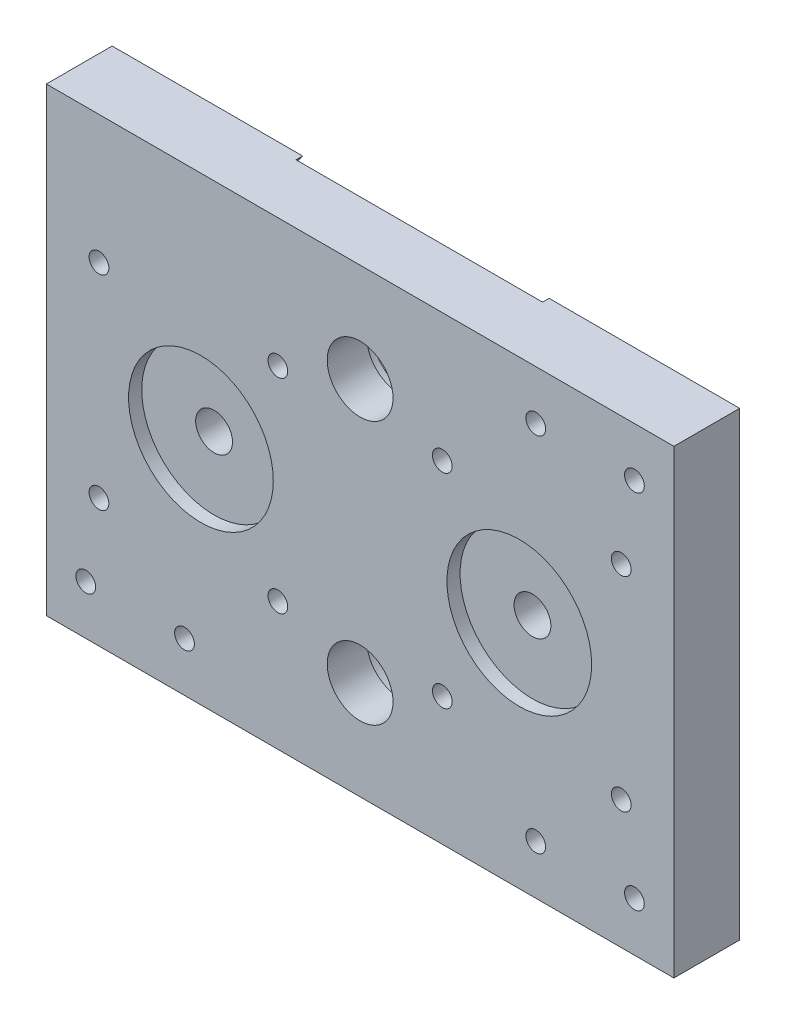
SolidWorks part; units mm, degrees
ref_plane "Front Plane" through (0, 0, 0) normal (0, 0, 1) x (1, 0, 0)
ref_plane "Top Plane" through (0, 0, 0) normal (0, 1, 0) x (1, 0, 0)
ref_plane "Right Plane" through (0, 0, 0) normal (1, 0, 0) x (0, 0, -1)
sketch "Sketch1" plane through (0, 0, 0) normal (0, 0, 1) x (1, 0, 0)
  line L0 (0, 0) -> (0, 40) construction
  line L2 (12.5, -15) -> (-12.5, -15)
  line L3 (12.5, -15) -> (12.5, 55)
  line L4 (12.5, 55) -> (-12.5, 55)
  line L5 (-12.5, -15) -> (-12.5, 55)
  line L6 (12.5, -15) -> (-12.5, 55) construction
  line L7 (12.5, 55) -> (-12.5, -15) construction
  circle A0 centre (0, 40) radius 7.9375
  circle A1 centre (0, 0) radius 7.9375
  point P5 (0, 20)
  dimension "D2" = 15.875
  dimension "D1" = 40
  dimension "D3" = 70
  dimension "D4" = 25
extrude "Boss-Extrude1" add sketch "Sketch1" along normal blind 10
sketch "Sketch2" plane through (0, 0, 10) normal (0, 0, 1) x (1, 0, 0)
  line L0 (12.5, 55) -> (-12.5, 55) construction
  line L1 (-47.7, 55) -> (-8.2, 55)
  line L3 (-47.7, -15) -> (-8.2, -15)
  line L4 (-8.2, 55) -> (-8.2, 36.9142)
  line L5 (-39.7, 35.5) -> (-8.7, 4.5) construction
  line L6 (-39.7, 4.5) -> (-8.7, 35.5) construction
  line L7 (-12.5, -15) -> (12.5, -15) construction
  line L8 (-8.2, 34.0858) -> (-8.2, 5.9142)
  line L9 (0, 55) -> (0, -15) construction
  line L10 (-8.7, 4.5) -> (-39.7, 4.5) construction
  line L11 (-8.7, 4.5) -> (-8.7, 35.5) construction
  line L12 (-8.7, 35.5) -> (-39.7, 35.5) construction
  line L13 (-39.7, 4.5) -> (-39.7, 35.5) construction
  line L14 (-8.7, 4.5) -> (-39.7, 35.5) construction
  line L15 (-8.7, 35.5) -> (-39.7, 4.5) construction
  line L16 (8.7, 35.5) -> (39.7, 4.5) construction
  line L17 (8.7, 4.5) -> (39.7, 35.5) construction
  line L18 (39.7, 4.5) -> (39.7, 35.5) construction
  line L19 (8.7, 35.5) -> (39.7, 35.5) construction
  line L20 (8.7, 4.5) -> (8.7, 35.5) construction
  line L21 (8.7, 4.5) -> (39.7, 4.5) construction
  line L22 (39.7, 4.5) -> (8.7, 35.5) construction
  line L23 (39.7, 35.5) -> (8.7, 4.5) construction
  line L24 (8.2, 55) -> (8.2, 36.9142)
  line L25 (47.7, -15) -> (8.2, -15)
  line L27 (47.7, 55) -> (8.2, 55)
  line L28 (-47.7, 55) -> (-47.7, -15)
  line L29 (47.7, 55) -> (47.7, -15)
  line L31 (-8.2, 3.0858) -> (-8.2, -15)
  line L32 (8.2, 3.0858) -> (8.2, -15)
  line L33 (8.2, 34.0858) -> (8.2, 5.9142)
  circle A0 centre (-39.7, 35.5) radius 1.5
  arc A1 (-8.2, 36.9142) -> (-8.2, 34.0858) centre (-8.7, 35.5) ccw
  arc A2 (-8.2, 5.9142) -> (-8.2, 3.0858) centre (-8.7, 4.5) ccw
  circle A3 centre (-39.7, 4.5) radius 1.5
  circle A4 centre (39.7, 4.5) radius 1.5
  arc A5 (8.2, 5.9142) -> (8.2, 3.0858) centre (8.7, 4.5) cw
  arc A6 (8.2, 36.9142) -> (8.2, 34.0858) centre (8.7, 35.5) cw
  circle A7 centre (39.7, 35.5) radius 1.5
  circle A8 centre (-24.2, 20) radius 2.8
  circle A9 centre (24.2, 20) radius 2.8
  point P0 (-24.2, 20)
  point P11 (-24.2, 20)
  point P34 (24.2, 20)
  dimension "D2" = 3
  dimension "D3" = 5.6
  dimension "D1" = 31
  dimension "D4" = 0.5
  dimension "D5" = 8
  dimension "D6" = 8.2
extrude "Boss-Extrude2" add sketch "Sketch2" against normal up to surface (10 mm away) up to face at (0, 20, 0)
sketch "Sketch6" plane through (0, 0, 10) normal (0, 0, 1) x (1, 0, 0)
  circle A0 centre (-12.5, 35.5) radius 1.5
  circle A1 centre (12.5, 35.5) radius 1.5
  circle A2 centre (-12.5, 4.5) radius 1.5
  circle A3 centre (12.5, 4.5) radius 1.5
  circle A5 centre (-39.7, 35.5) radius 1.5 construction
extrude "Cut-Extrude3" cut sketch "Sketch6" against normal up to surface (10 mm away) up to face at (0, 20, 0)
sketch "Sketch3" plane through (0, 0, 10) normal (0, 0, 1) x (1, 0, 0)
  circle A0 centre (0, 40) radius 7.9375
  circle A1 centre (0, 0) radius 7.9375
  circle A2 centre (0, 40) radius 7.9375 construction
  circle A3 centre (0, 40) radius 5
  circle A4 centre (0, 0) radius 5
  circle A8 centre (0, 0) radius 7.9375 construction
  dimension "D1" = 10
extrude "Boss-Extrude3" add sketch "Sketch3" against normal blind 6.0216
sketch "Sketch4" plane through (0, 0, 10) normal (0, 0, 1) x (1, 0, 0)
  circle A0 centre (-24.2, 20) radius 11
  circle A1 centre (24.2, 20) radius 11
  dimension "D1" = 22
extrude "Cut-Extrude1" cut sketch "Sketch4" against normal blind 2
sketch "Sketch5" plane through (0, 0, 0) normal (0, 0, -1) x (-1, 0, 0)
  circle A0 centre (-39.7, 35.5) radius 2.75
  circle A1 centre (-12.5, 35.5) radius 2.75
  circle A2 centre (-39.7, 4.5) radius 2.75
  circle A3 centre (-12.5, 4.5) radius 2.75
  circle A4 centre (12.5, 35.5) radius 2.75
  circle A5 centre (39.7, 35.5) radius 2.75
  circle A6 centre (12.5, 4.5) radius 2.75
  circle A7 centre (39.7, 4.5) radius 2.75
  circle A9 centre (12.5, 4.5) radius 1.5 construction
  circle A10 centre (-12.5, 4.5) radius 1.5 construction
  circle A11 centre (-12.5, 35.5) radius 1.5 construction
  circle A12 centre (12.5, 35.5) radius 1.5 construction
  dimension "D1" = 5.5
extrude "Cut-Extrude2" cut sketch "Sketch5" against normal blind 3.1
sketch "Sketch11" plane through (0, 0, 0) normal (0, 0, -1) x (-1, 0, 0)
  circle A0 centre (-24.2, 20) radius 10.2
  circle A1 centre (24.2, 20) radius 10.2
  dimension "D1" = 20.4
extrude "Cut-Extrude6" cut sketch "Sketch11" against normal blind 2
sketch "Sketch12" plane through (0, 0, 0) normal (0, 0, -1) x (-1, 0, 0)
  circle A0 centre (24.2, 20) radius 12.5
  dimension "D1" = 25
extrude "Cut-Extrude8" cut sketch "Sketch12" against normal up to surface (2 mm away) up to face at (-34.4, 20, 2)
sketch "Sketch13" plane through (0, 0, 10) normal (0, 0, 1) x (1, 0, 0)
  line L0 (-39.7, 4.5) -> (-41.7, -7.5) construction
  line L1 (-41.7, -7.5) -> (-26.7, -7.5) construction
  line L2 (-26.7, -7.5) -> (-25.8262, -6.2808) construction
  line L3 (25.8262, -6.2808) -> (26.7, -7.5) construction
  line L4 (26.7, -7.5) -> (41.7, -7.5) construction
  line L5 (41.7, -7.5) -> (39.7, 4.5) construction
  line L6 (26.9466, 46.0204) -> (26.7, 47.5) construction
  line L7 (26.7, 47.5) -> (41.7, 47.5) construction
  line L8 (41.7, 47.5) -> (42.5738, 46.2808) construction
  line L9 (-47.7, 55) -> (-47.7, -15) construction
  line L10 (47.7, -15) -> (47.7, 55) construction
  circle A0 centre (-41.7, -7.5) radius 1.5
  circle A1 centre (-26.7, -7.5) radius 1.5
  circle A2 centre (26.7, -7.5) radius 1.5
  circle A3 centre (41.7, -7.5) radius 1.5
  circle A4 centre (26.7, 47.5) radius 1.5
  circle A5 centre (41.7, 47.5) radius 1.5
  dimension "D1" = 3
  dimension "D2" = 15
  dimension "D3" = 15
  dimension "D4" = 12
  dimension "D5" = 6
  dimension "D6" = 6
  dimension "D7" = 55
extrude "Cut-Extrude9" cut sketch "Sketch13" against normal up to surface (10 mm away) up to face at (-36.7, 20, 0)
sketch "Sketch14" plane through (0, 0, 0) normal (0, 0, -1) x (-1, 0, 0)
  circle A0 centre (0, 40) radius 24
  dimension "D1" = 48
extrude "Cut-Extrude10" cut sketch "Sketch14" against normal blind 1
